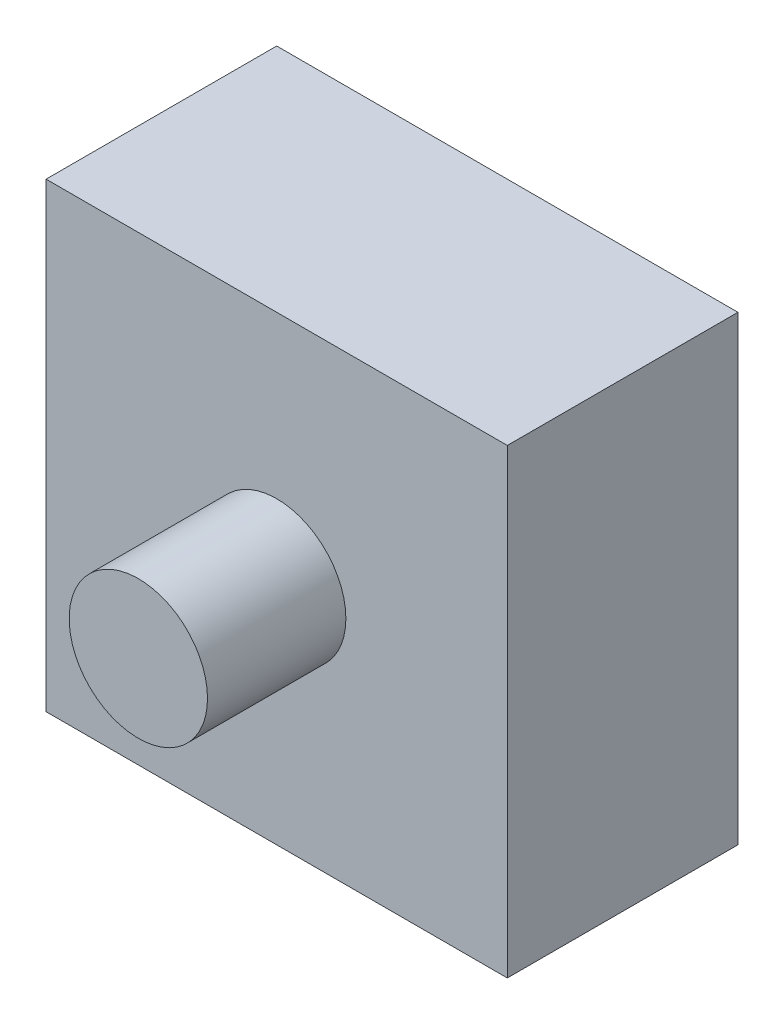
SolidWorks part; units mm, degrees
ref_plane "Front Plane" through (0, 0, 0) normal (0, 0, 1) x (1, 0, 0)
ref_plane "Top Plane" through (0, 0, 0) normal (0, 1, 0) x (1, 0, 0)
ref_plane "Right Plane" through (0, 0, 0) normal (1, 0, 0) x (0, 0, -1)
sketch "Sketch1" plane through (0, 0, 0) normal (0, 0, 1) x (1, 0, 0)
  line L1 (-50, 50) -> (50, 50)
  line L2 (-50, 50) -> (-50, -50)
  line L3 (-50, -50) -> (50, -50)
  line L4 (50, 50) -> (50, -50)
  point P5 (-50, 0)
  point P6 (0, 50)
  dimension "D1" = 100
  dimension "D2" = 100
  dimension "D3" = 50
  dimension "D4" = 50
extrude "Boss-Extrude1" add sketch "Sketch1" along normal blind 50
sketch "Sketch2" plane through (0, 0, 50) normal (0, 0, 1) x (1, 0, 0)
  circle A0 centre (0, 0) radius 15
  dimension "D1" = 30
extrude "Boss-Extrude2" add sketch "Sketch2" along normal blind 30
